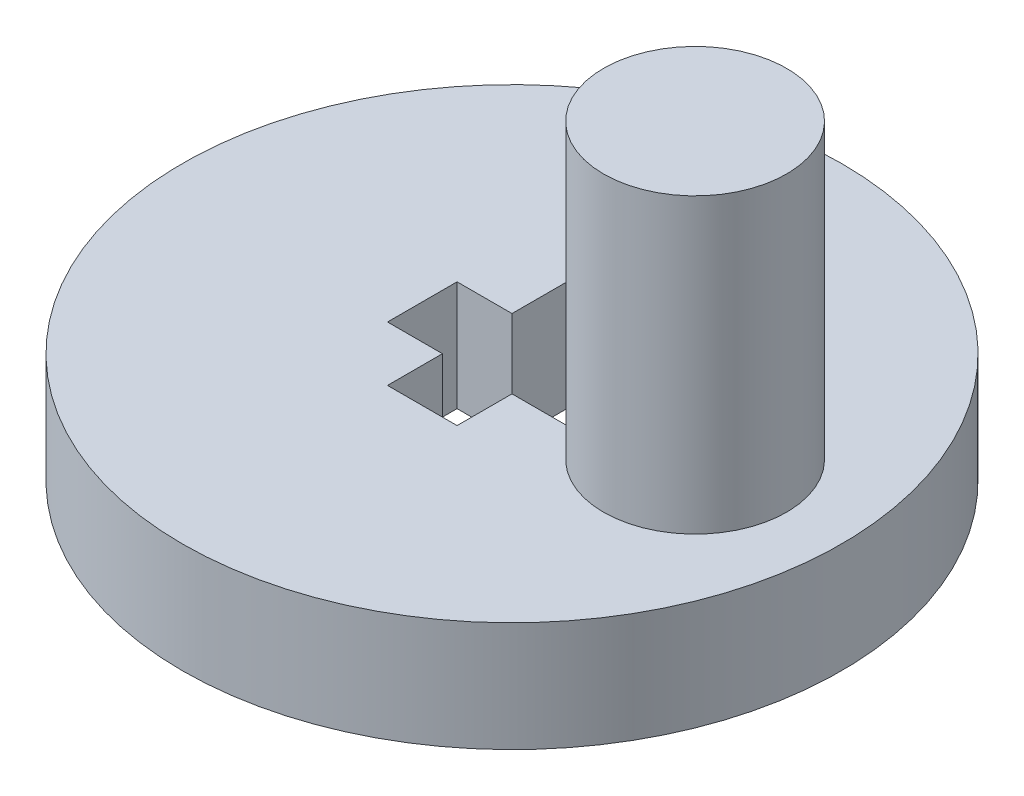
SolidWorks part; units mm, degrees
ref_plane "Front Plane" through (0, 0, 0) normal (0, 0, 1) x (1, 0, 0)
ref_plane "Top Plane" through (0, 0, 0) normal (0, 1, 0) x (1, 0, 0)
ref_plane "Right Plane" through (0, 0, 0) normal (1, 0, 0) x (0, 0, -1)
sketch "Sketch1" plane through (0, 0, 0) normal (0, 1, 0) x (1, 0, 0)
  line L6 (-2.45, 0.95) -> (-2.45, -0.95)
  line L7 (-2.45, -0.95) -> (-0.95, -0.95)
  line L8 (-0.95, -0.95) -> (-0.95, -2.45)
  line L9 (-0.95, -2.45) -> (0.95, -2.45)
  line L10 (0.95, -2.45) -> (0.95, -0.95)
  line L11 (0.95, -0.95) -> (2.45, -0.95)
  line L12 (2.45, -0.95) -> (2.45, 0.95)
  line L13 (2.45, 0.95) -> (0.95, 0.95)
  line L14 (0.95, 0.95) -> (0.95, 2.45)
  line L15 (0.95, 2.45) -> (-0.95, 2.45)
  line L16 (-0.95, 2.45) -> (-0.95, 0.95)
  line L17 (-0.95, 0.95) -> (-2.45, 0.95)
  circle A0 centre (0, 0) radius 9
  circle A2 centre (0, 0) radius 2.6277 construction
  dimension "D1" = 18
  dimension "D4" = 1.5
  dimension "D5" = 1.9
extrude "Boss-Extrude1" add sketch "Sketch1" along normal blind 3
sketch "Sketch2" plane through (0, 3, 0) normal (0, 1, 0) x (1, 0, 0)
  circle A0 centre (5, 0) radius 2.5
  dimension "D2" = 5
  dimension "D1" = 5
extrude "Boss-Extrude2" add sketch "Sketch2" along normal blind 8
sketch "Sketch5" plane through (0, 3, 0) normal (0, 1, 0) x (1, 0, 0)
  line L0 (-2.25, 0.9) -> (-2.25, -0.9)
  line L1 (-2.25, -0.9) -> (-0.9, -0.9)
  line L2 (-0.9, -0.9) -> (-0.9, -2.25)
  line L3 (-0.9, -2.25) -> (0.9, -2.25)
  line L4 (0.9, -2.25) -> (0.9, -0.9)
  line L5 (0.9, -0.9) -> (2.25, -0.9)
  line L6 (2.25, -0.9) -> (2.25, 0.9)
  line L7 (2.25, 0.9) -> (0.9, 0.9)
  line L8 (0.9, 0.9) -> (0.9, 2.25)
  line L9 (0.9, 2.25) -> (-0.9, 2.25)
  line L10 (-0.9, 2.25) -> (-0.9, 0.9)
  line L11 (-0.9, 0.9) -> (-2.25, 0.9)
  line L36 (2.75, 0.9) -> (2.75, -0.9)
  line L37 (2.75, -0.9) -> (4.1, -0.9)
  line L38 (4.1, -0.9) -> (4.1, -2.25)
  line L39 (4.1, -2.25) -> (5.9, -2.25)
  line L40 (5.9, -2.25) -> (5.9, -0.9)
  line L41 (5.9, -0.9) -> (7.25, -0.9)
  line L42 (7.25, -0.9) -> (7.25, 0.9)
  line L43 (7.25, 0.9) -> (5.9, 0.9)
  line L44 (5.9, 0.9) -> (5.9, 2.25)
  line L45 (5.9, 2.25) -> (4.1, 2.25)
  line L46 (4.1, 2.25) -> (4.1, 0.9)
  line L47 (4.1, 0.9) -> (2.75, 0.9)
  circle A0 centre (0, 0) radius 2.4233 construction
  circle A1 centre (5, 0) radius 2.4233 construction
  circle A2 centre (0, 0) radius 9.1
  dimension "D2" = 1.35
  dimension "D3" = 1.8
  dimension "D1" = 1.35
  dimension "D4" = 1.8
  dimension "D5" = 5
